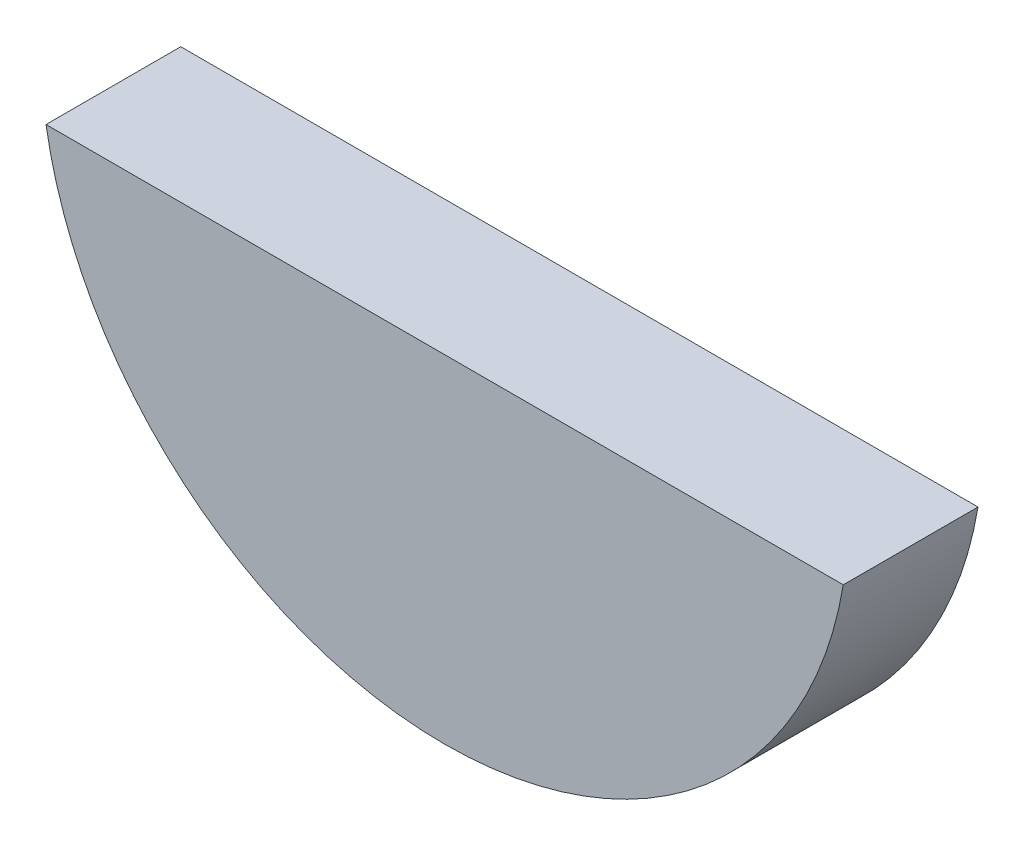
SolidWorks part; units mm, degrees
material "Plain Carbon Steel"
ref_plane "Front" through (0, 0, 0) normal (0, 0, 1) x (1, 0, 0)
ref_plane "Top" through (0, 0, 0) normal (0, 1, 0) x (1, 0, 0)
ref_plane "Right" through (0, 0, 0) normal (1, 0, 0) x (0, 0, -1)
sketch "Sketch1" plane through (0, 0, 0) normal (0, 0, 1) x (1, 0, 0)
  line L0 (-9.6561, 0) -> (11.5414, 0) construction
  line L1 (-9.3939, -1.5748) -> (9.3939, -1.5748)
  line L2 (0, -9.525) -> (0, 6.4141) construction
  line L3 (-9.6561, -1.5748) -> (9.3939, -1.5748) construction
  line L5 (-9.6561, 0) -> (9.3939, 0) construction
  arc A0 (-9.3939, -1.5748) -> (9.3939, -1.5748) centre (0, 0) ccw
  dimension "D1" = 9.525
  dimension "D2" = 7.9502
  dimension "D3" = 1.5748
extrude "Boss-Extrude1" add sketch "Sketch1" along normal mid plane 3.175
